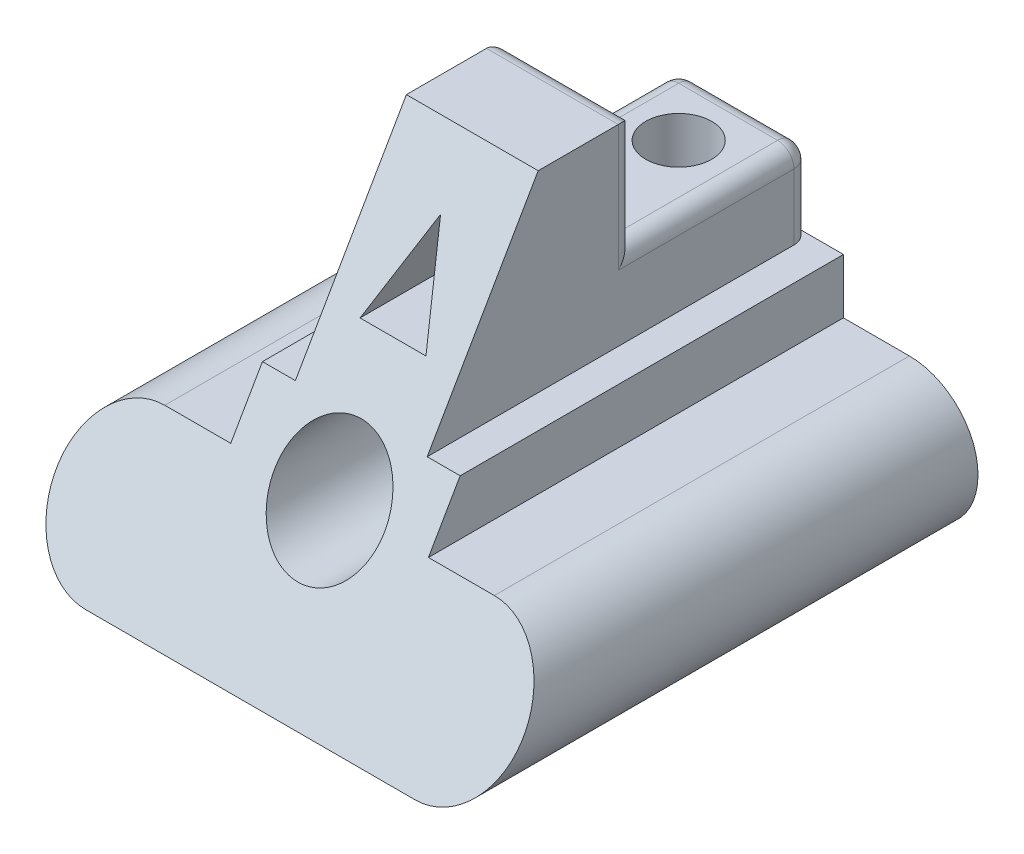
SolidWorks part; units mm, degrees
ref_plane "Front Plane" through (0, 0, 0) normal (0, 0, 1) x (1, 0, 0)
ref_plane "Top Plane" through (0, 0, 0) normal (0, 1, 0) x (1, 0, 0)
ref_plane "Right Plane" through (0, 0, 0) normal (1, 0, 0) x (0, 0, -1)
sketch "Sketch1" plane through (0, 0, 0) normal (0, 0, 1) x (1, 0, 0)
  line L12 (0, 0) -> (60, 0) construction
  line L13 (0, 12.5) -> (12, 12.5)
  line L14 (0, -12.5) -> (60, -12.5)
  line L15 (12, 12.5) -> (12, 22.5)
  line L16 (12, 22.5) -> (18, 22.5)
  line L17 (18, 22.5) -> (18, 57.5)
  line L18 (18, 57.5) -> (42, 57.5)
  line L19 (42, 57.5) -> (42, 22.5)
  line L20 (42, 22.5) -> (48, 22.5)
  line L21 (48, 22.5) -> (48, 12.5)
  line L22 (48, 12.5) -> (60, 12.5)
  line L23 (24, 32.5) -> (36, 32.5)
  line L24 (36, 32.5) -> (30, 47.5)
  line L25 (30, 47.5) -> (24, 32.5)
  line L26 (30, 57.5) -> (30, -12.5) construction
  arc A0 (0, 12.5) -> (0, -12.5) centre (0, 0) ccw
  arc A1 (60, -12.5) -> (60, 12.5) centre (60, 0) ccw
  circle A2 centre (30, 12.5) radius 10
  point P2 (30, 0)
  dimension "D2" = 12.5
  dimension "D13" = 20
  dimension "D1" = 60
  dimension "D3" = 70
  dimension "D4" = 10
  dimension "D5" = 12
  dimension "D6" = 24
  dimension "D7" = 6
  dimension "D8" = 10
  dimension "D9" = 12
  dimension "D10" = 36
  dimension "D11" = 35
  dimension "D12" = 35
  dimension "D14" = 25
  dimension "D15" = 18
  dimension "D16" = 15
  dimension "D17" = 12
  dimension "D18" = 6
  dimension "D19" = 12
  dimension "D20" = 45
extrude "Boss-Extrude1" add sketch "Sketch1" against normal blind 90
sketch "Sketch3" plane through (48, 0, 0) normal (1, 0, 0) x (0, 0, -1)
  line L0 (0, -12.5) -> (40.4145, 57.5)
  line L1 (90, 57.5) -> (0, 57.5) construction
  line L2 (0, 12.5) -> (0, -12.5) construction
  dimension "D1" = 30
extrude "Cut-Extrude2" cut sketch "Sketch3" against normal through all and the other way through all
sketch "Sketch4" plane through (18, 0, 0) normal (-1, 0, 0) x (0, 0, 1)
  line L1 (-90, 57.5) -> (-58, 57.5)
  line L2 (-90, 57.5) -> (-90, 37.5)
  line L3 (-90, 37.5) -> (-58, 37.5)
  line L4 (-58, 57.5) -> (-58, 37.5)
  dimension "D1" = 20
  dimension "D2" = 32
extrude "Cut-Extrude3" cut sketch "Sketch4" against normal through all
sketch "Sketch5" plane through (0, 37.5, 0) normal (0, 1, 0) x (1, 0, 0)
  line L1 (18, 90) -> (42, 90)
  line L2 (18, 90) -> (18, 58)
  line L3 (18, 58) -> (42, 58)
  line L4 (42, 90) -> (42, 58)
extrude "Boss-Extrude2" add sketch "Sketch5" against normal blind 5
hole_wizard "Ø1.5mm Dowel Hole1" positions "Sketch6" profile "Sketch8" hole size "Ø1.5" standard "ANSI Metric" end condition through all
sketch "Sketch6" plane through (0, 37.5, 0) normal (0, 1, 0) x (1, 0, 0)
  line L0 (42, 58) -> (42, 90) construction
  line L1 (18, 90) -> (42, 90) construction
  point P0 (30, 78)
  dimension "D1" = 12
  dimension "D2" = 12
sketch "Sketch8" plane through (30, 37.5, -78) normal (1, 0, 0) x (0, 0, 1)
  line L0 (0, 0) -> (0, 50)
  line L1 (0, 50) -> (6, 50)
  line L2 (6, 50) -> (6, 0)
  line L5 (6, 0) -> (0, 0)
  line L11 (0, -6.35) -> (0, 107.95) construction
  dimension "Thru Hole Dia." = 12
  dimension "Thru Hole Depth" = 50
fillet "Fillet1" radius 3 8 edges at (30, 57.5, -58) (42, 47.5, -58) (42, 37.5, -74) (42, 30, -90) (18, 30, -90) (30, 37.5, -90) (18, 47.5, -58) (18, 37.5, -74)
